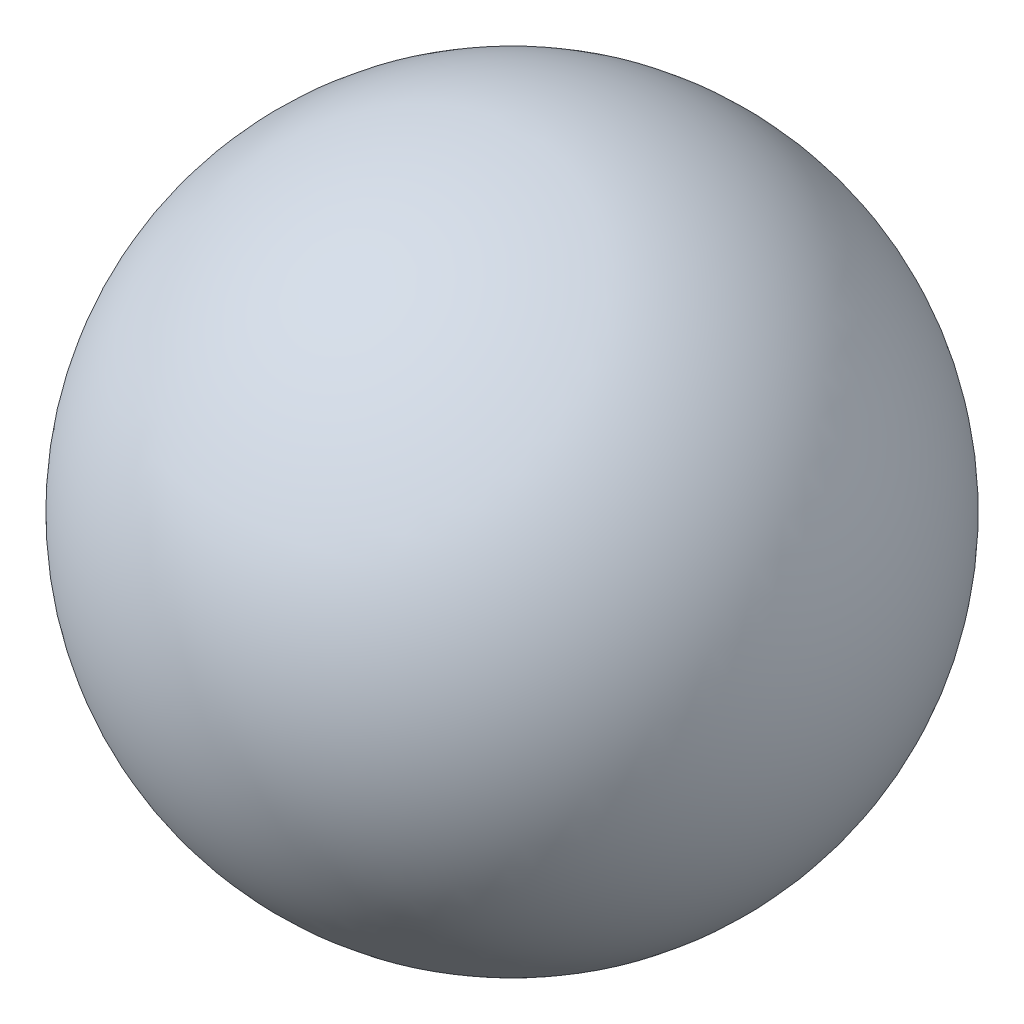
SolidWorks part; units mm, degrees
ref_plane "Ebene vorne" through (0, 0, 0) normal (0, 0, 1) x (1, 0, 0)
ref_plane "Ebene oben" through (0, 0, 0) normal (0, 1, 0) x (1, 0, 0)
ref_plane "Ebene rechts" through (0, 0, 0) normal (1, 0, 0) x (0, 0, -1)
sketch "Skizze1" plane through (0, 0, 0) normal (0, 0, 1) x (1, 0, 0)
  line L0 (1.875, -1.25) -> (0, -1.25)
  line L1 (-5, -5) -> (5, -5) construction
  line L2 (-5, -5) -> (-5, 5) construction
  line L3 (-5, 5) -> (5, 5) construction
  line L4 (5, -5) -> (5, 5) construction
  line L5 (-5, -5) -> (5, 5) construction
  line L6 (-5, 5) -> (5, -5) construction
  line L7 (0, -1.25) -> (0, 1.25) construction
  line L8 (0, 1.25) -> (1.875, 1.25)
  line L9 (1.875, -2.5) -> (-5, -2.5)
  line L10 (-5, -2.5) -> (-5, -5)
  line L11 (-5, -5) -> (1.875, -5)
  line L12 (0, -1.25) -> (-1.875, -1.25)
  line L13 (-1.875, 5) -> (5, 5)
  line L14 (5, 5) -> (5, 2.5)
  line L15 (5, 2.5) -> (-1.875, 2.5)
  line L16 (-1.875, 1.25) -> (0, 1.25)
  line L17 (0, 2.5) -> (0, 0) construction
  line L18 (0, 0) -> (0, -2.5) construction
  arc A0 (1.875, 1.25) -> (1.875, -5) centre (1.875, -1.875) cw
  arc A1 (1.875, -1.25) -> (1.875, -2.5) centre (1.875, -1.875) cw
  arc A2 (-1.875, -1.25) -> (-1.875, 5) centre (-1.875, 1.875) cw
  arc A3 (-1.875, 2.5) -> (-1.875, 1.25) centre (-1.875, 1.875) ccw
  point P0 (0, 0)
  dimension "D1" = 10
extrude "Aufsatz-Linear austragen1" add sketch "Skizze1" along normal mid plane 5
sketch "Skizze2" plane through (0, 0, 0) normal (0, 0, 1) x (1, 0, 0)
  line L0 (0, 10) -> (0, -10)
  arc A0 (0, 10) -> (0, -10) centre (0, 0) ccw
  dimension "D1" = 20
revolve "Rotation1" add sketch "Skizze2" angle 360 about L0
